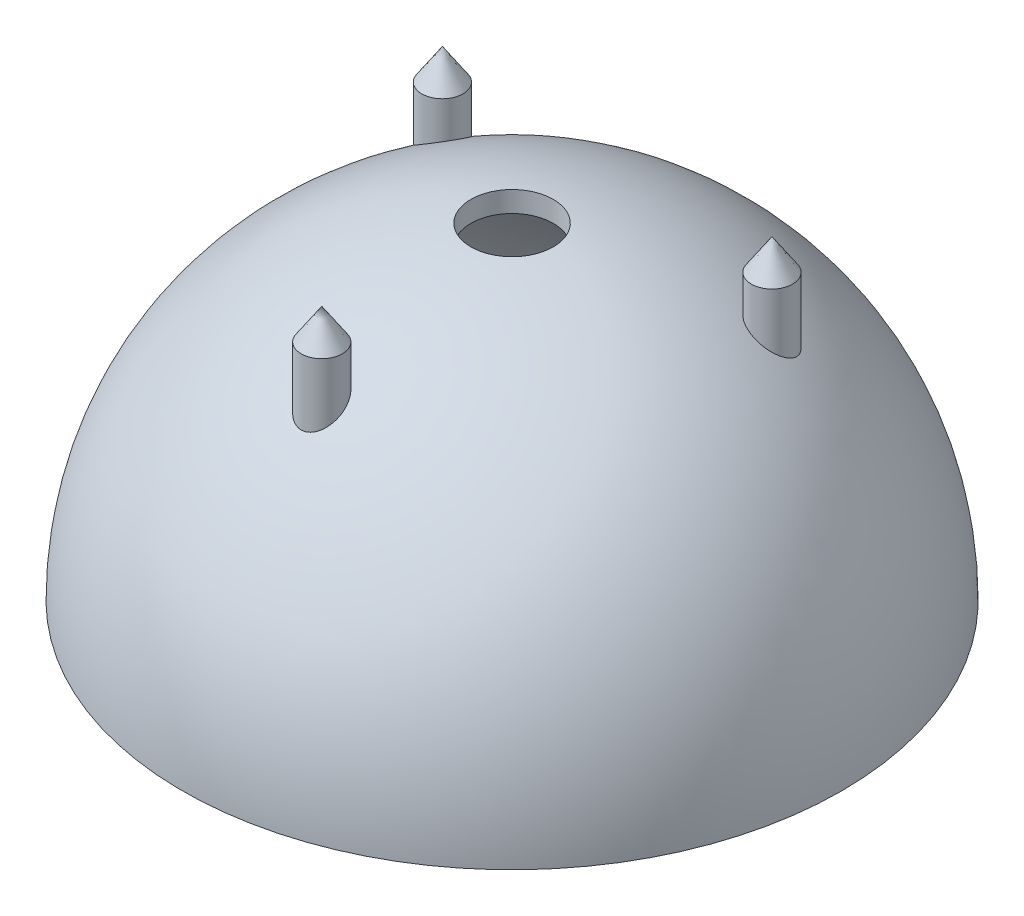
SolidWorks part; units mm, degrees
ref_plane "Front Plane" through (0, 0, 0) normal (0, 0, 1) x (1, 0, 0)
ref_plane "Top Plane" through (0, 0, 0) normal (0, 1, 0) x (1, 0, 0)
ref_plane "Right Plane" through (0, 0, 0) normal (1, 0, 0) x (0, 0, -1)
sketch "Sketch1" plane through (0, 0, 0) normal (0, 0, 1) x (1, 0, 0)
  line L0 (0, 0) -> (38.1, 0) construction
  line L1 (0, 38.1) -> (0, 0) construction
  line L2 (38.1, 0) -> (40.64, 0)
  line L3 (0, 38.1) -> (0, 40.64)
  arc A0 (0, 38.1) -> (38.1, 0) centre (0, 0) cw
  arc A1 (40.64, 0) -> (0, 40.64) centre (0, 0) ccw
  dimension "D1" = 38.1
  dimension "D2" = 2.54
revolve "Revolve1" add sketch "Sketch1" angle 360 about L3
ref_plane "Plane1" through (0, 39.37, 0) normal (0, -1, 0) x (1, 0, 0)
sketch "Sketch2" plane through (0, 39.37, 0) normal (0, -1, 0) x (1, 0, 0)
  line L1 (0, 23.4635) -> (20.32, -11.7318) construction
  line L2 (20.32, -11.7318) -> (-20.32, -11.7318) construction
  line L3 (-20.32, -11.7318) -> (0, 23.4635) construction
  line L4 (0, 0) -> (0, -11.7318) construction
  line L5 (0, 0) -> (10.16, 5.8659) construction
  line L6 (0, 0) -> (-10.16, 5.8659) construction
  circle A0 centre (0, 23.4635) radius 2.54
  circle A1 centre (-20.32, -11.7318) radius 2.54
  circle A2 centre (20.32, -11.7318) radius 2.54
  dimension "D2" = 5.08
  dimension "D1" = 40.64
extrude "Extrude1" add sketch "Sketch2" along normal up to surface (9.4598 mm away)
sketch "Sketch4" plane through (0, 0, 0) normal (0, -1, 0) x (1, 0, 0)
  circle A0 centre (0, 0) radius 5.08
  dimension "D1" = 10.16
extrude "Extrude3" cut sketch "Sketch4" against normal through all
sketch "Sketch5" plane through (0, 0, 0) normal (1, 0, 0) x (0, 0, -1)
  line L0 (-20.9235, 39.37) -> (-23.4635, 43.18)
  line L1 (-20.9235, 39.37) -> (-23.4635, 39.37)
  line L2 (-20.9235, 39.37) -> (-26.0035, 39.37) construction
  line L3 (-23.4635, 39.37) -> (-23.4635, 43.18) construction
  line L4 (-23.4635, 43.18) -> (-23.4635, 39.37)
  dimension "D1" = 3.81
revolve "Revolve2" add sketch "Sketch5" angle 360 about L3
pattern_circular "CirPattern1" count 3 every 120 about axis through (0, 0, 0) along (0, 1, 0) of "Revolve2"
